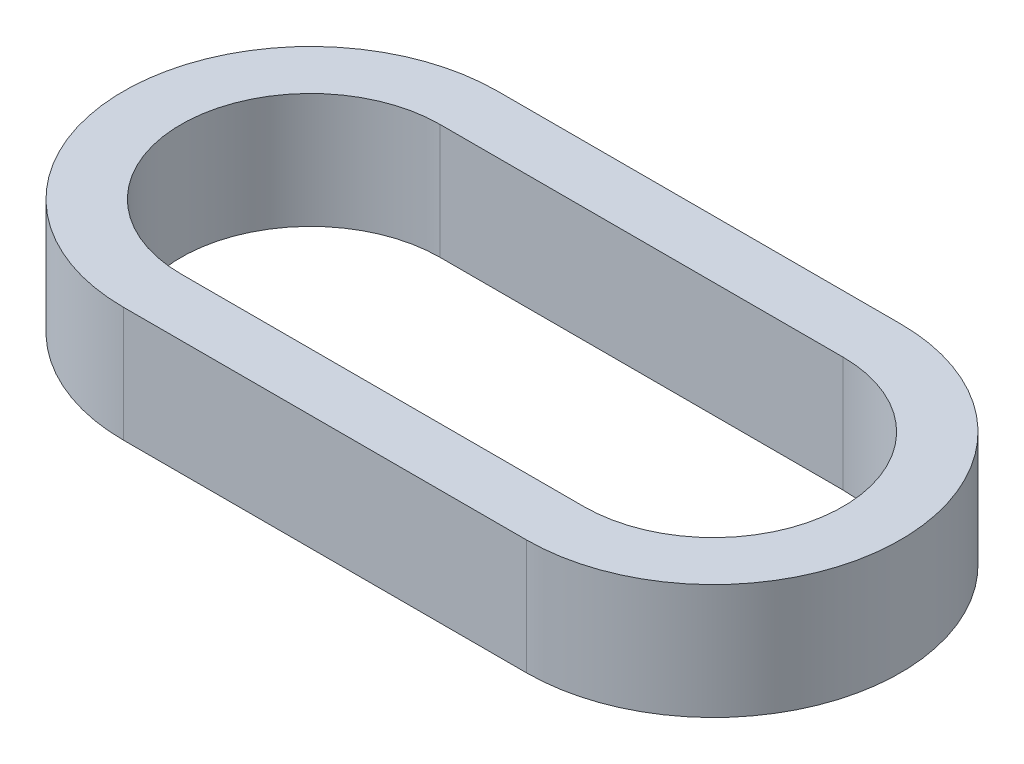
SolidWorks part; units mm, degrees
material "uhlíková ocel 7850"
ref_plane "Přední rovina" through (0, 0, 0) normal (0, 0, 1) x (1, 0, 0)
ref_plane "Horní rovina" through (0, 0, 0) normal (0, 1, 0) x (1, 0, 0)
ref_plane "Pravá rovina" through (0, 0, 0) normal (1, 0, 0) x (0, 0, -1)
sketch "Skica1" plane through (0, 0, 0) normal (0, 1, 0) x (1, 0, 0)
  line L0 (-3.5, 0) -> (3.5, 0) construction
  line L1 (-3.5, 2.25) -> (3.5, 2.25)
  line L2 (-3.5, -2.25) -> (3.5, -2.25)
  arc A0 (-3.5, 2.25) -> (-3.5, -2.25) centre (-3.5, 0) ccw
  arc A1 (3.5, -2.25) -> (3.5, 2.25) centre (3.5, 0) ccw
  point P2 (0, 0)
  dimension "D1" = 7
  dimension "D2" = 4.5
extrude "Vysunout tenkostěnný1" add sketch "Skica1" along normal blind 2 thin thin type one direction wall 1
